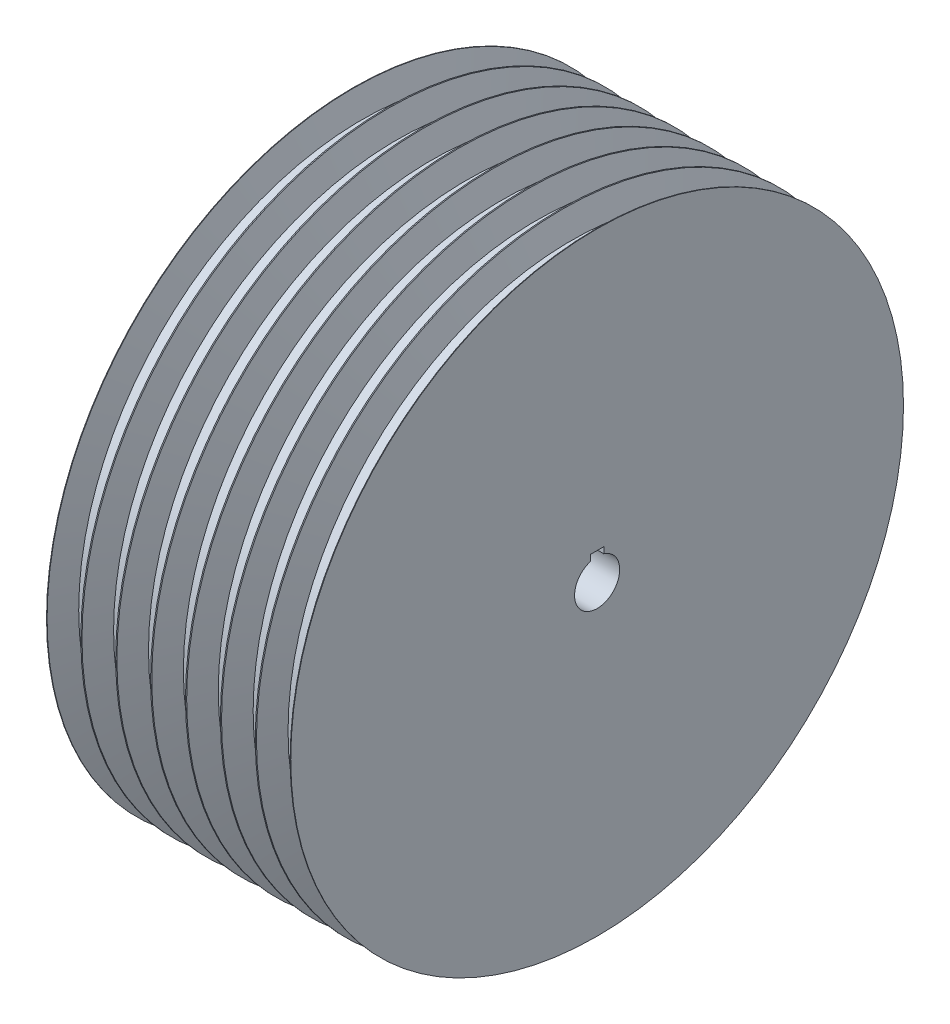
SolidWorks part; units mm, degrees
ref_plane "Front Plane" through (0, 0, 0) normal (0, 0, 1) x (1, 0, 0)
ref_plane "Top Plane" through (0, 0, 0) normal (0, 1, 0) x (1, 0, 0)
ref_plane "Right Plane" through (0, 0, 0) normal (1, 0, 0) x (0, 0, -1)
sketch "Sketch1" plane through (0, 0, 0) normal (0, 0, 1) x (1, 0, 0)
  line L0 (-3.1725, 0) -> (3.1725, 0)
  line L1 (3.1725, 0) -> (6.35, 8.73)
  line L2 (6.35, 8.73) -> (6.5714, 8.73)
  line L3 (-3.1725, 0) -> (-6.35, 8.73)
  line L4 (-6.35, 8.73) -> (-6.5714, 8.73)
  line L5 (-3.1725, 0) -> (0, -8.7165) construction
  line L6 (0, -8.7165) -> (3.1725, 0) construction
  line L7 (0, -8.7165) -> (0, 0) construction
  line L8 (-6.5714, 8.73) -> (-6.5714, -106.68)
  line L9 (-6.5714, -106.68) -> (6.5714, -106.68)
  line L10 (6.5714, -106.68) -> (6.5714, 8.73)
  point P4 (0, 0)
  dimension "D1" = 40
  dimension "D2" = 8.73
  dimension "D3" = 12.7
  dimension "D4" = 0.2214
  dimension "D5" = 106.68
revolve "Revolve1" add sketch "Sketch1" angle 360 about L9
pattern_linear "LPattern1" count 7 spacing 13.1427 along (1, 0, 0) of bodies 101
sketch "Sketch2" plane through (85.4276, 0, 0) normal (1, 0, 0) x (0, 0, -1)
  circle A0 centre (0, -106.68) radius 8.5
  circle A1 centre (0, -106.68) radius 115.41 construction
  dimension "D1" = 17
extrude "Cut-Extrude1" cut sketch "Sketch2" against normal through all
sketch "Sketch3" plane through (85.4276, 0, 0) normal (1, 0, 0) x (0, 0, -1)
  line L0 (0, -98.18) -> (0, -106.68) construction
  line L1 (-2.5, -98.556) -> (2.5, -98.556)
  line L2 (-2.5, -98.556) -> (-2.5, -96.256)
  line L3 (-2.5, -96.256) -> (2.5, -96.256)
  line L4 (2.5, -98.556) -> (2.5, -96.256)
  circle A0 centre (0, -106.68) radius 8.5 construction
  dimension "D1" = 2.3
  dimension "D2" = 5
extrude "Cut-Extrude2" cut sketch "Sketch3" against normal blind 10
